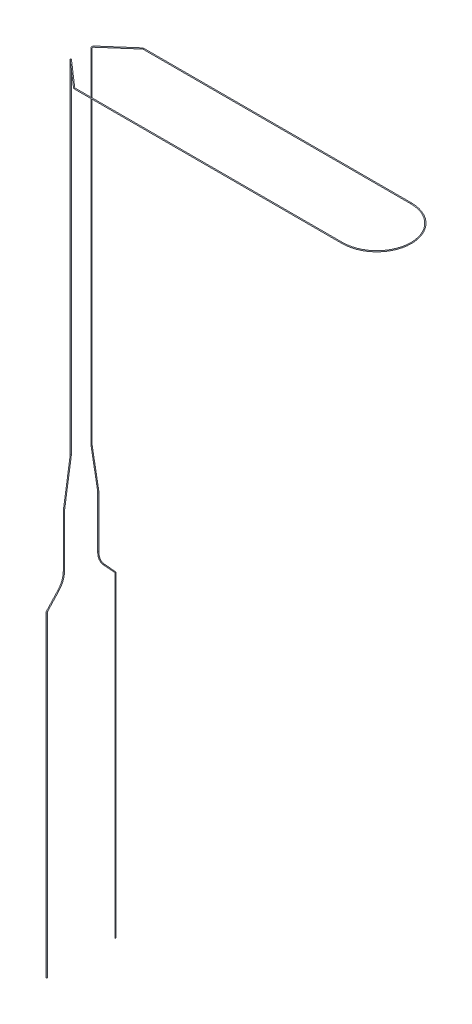
SolidWorks part; units mm, degrees
ref_plane "Plan de face" through (0, 0, 0) normal (0, 0, 1) x (1, 0, 0)
ref_plane "Plan de dessus" through (0, 0, 0) normal (0, 1, 0) x (1, 0, 0)
ref_plane "Plan de droite" through (0, 0, 0) normal (1, 0, 0) x (0, 0, -1)
sketch3d "Esquisse3D1"
  line L0 (0, 0, 0) -> (0, 0, 10.3571) construction
  line L6 (0, 255, 6) -> (0, 56.7647, 6)
  line L7 (0, 256, 6) -> (0, 256, 20) construction
  line L10 (0, 256, 20) -> (16, 256, 20) construction
  line L11 (0.7526, 256, 6.6585) -> (15.7172, 256, 19.7526)
  line L12 (0, 0, 0) -> (0, 256, 0) construction
  line L13 (16.3757, 256, 20) -> (172, 256, 20)
  line L14 (0, 256, 0) -> (219.9657, 256, 0) construction
  line L15 (0, 0, 5.3828) -> (0, -8.4495, 13.1824) construction
  line L16 (0, 0, 13.1824) -> (0, -8.4495, 13.1824) construction
  line L17 (0, -8.4495, 13.1824) -> (0, -15.5477, 19.7348)
  line L18 (0, 0, 10) -> (0, -0.31, 10)
  line L19 (0, -16.226, 20) -> (0, -200, 20)
  line L20 (0, 0, 10) -> (0, 29.2353, 10)
  line L21 (0, 30.7558, 9.8837) -> (0, 55.2442, 6.1163)
  line L22 (0, 0, -13.1824) -> (0, -8.4495, -13.1824) construction
  line L23 (0, 0, -5.3828) -> (0, -8.4495, -13.1824) construction
  line L24 (0, 256, -20) -> (16, 256, -20) construction
  line L25 (0, 256, -6) -> (0, 256, -20) construction
  line L26 (0, 30.7558, -9.8837) -> (0, 55.2442, -6.1163)
  line L27 (0, 0, -10) -> (0, 29.2353, -10)
  line L28 (0, -16.226, -20) -> (0, -200, -20)
  line L29 (0, 0, -10) -> (0, -0.31, -10)
  line L30 (0, -8.4495, -13.1824) -> (0, -15.5477, -19.7348)
  line L31 (16.3757, 256, -20) -> (172, 256, -20)
  line L32 (0.7526, 256, -6.6585) -> (15.7172, 256, -19.7526)
  line L33 (0, 255, -6) -> (0, 56.7647, -6)
  arc A0 (172, 256, 20) -> (172, 256, -20) centre (172, 256, 0) ccw
  circle A2 centre (20, 256, 20) radius 4 construction
  arc A3 (0, -0.31, 10) -> (0, -8.4495, 13.1824) centre (0, -0.31, 22) ccw
  arc A4 (16.3757, 256, 20) -> (15.7172, 256, 19.7526) centre (16.3757, 256, 19) ccw
  arc A5 (0, 29.2353, 10) -> (0, 30.7558, 9.8837) centre (0, 29.2353, 0) ccw
  arc A6 (0, -15.5477, 19.7348) -> (0, -16.226, 20) centre (0, -16.226, 19) ccw
  arc A7 (0, 56.7647, 6) -> (0, 55.2442, 6.1163) centre (0, 56.7647, 16) ccw
  arc A8 (0.7526, 256, 6.6585) -> (0, 255, 6) centre (0.7526, 255, 6.6585) ccw
  circle A9 centre (20, 256, -20) radius 4 construction
  arc A10 (0, 255, -6) -> (0.7526, 256, -6.6585) centre (0.7526, 255, -6.6585) cw
  arc A11 (0, 55.2442, -6.1163) -> (0, 56.7647, -6) centre (0, 56.7647, -16) cw
  arc A12 (0, -16.226, -20) -> (0, -15.5477, -19.7348) centre (0, -16.226, -19) cw
  arc A13 (0, 30.7558, -9.8837) -> (0, 29.2353, -10) centre (0, 29.2353, 0) cw
  arc A14 (15.7172, 256, -19.7526) -> (16.3757, 256, -20) centre (16.3757, 256, -19) cw
  arc A15 (0, -8.4495, -13.1824) -> (0, -0.31, -10) centre (0, -0.31, -22) cw
  point P13 (172, 276, 0)
  point P22 (20, 260, 20)
  point P25 (-12, -0.31, 22)
  point P28 (0, 30, 10)
  point P29 (16, 256, 20)
  point P31 (16.3757, 255, 19)
  point P34 (-10, 29.2353, 0)
  point P39 (0, -15.835, 20)
  point P40 (1, -16.226, 19)
  point P42 (0, 56, 6)
  point P44 (-10, 56.7647, 16)
  point P47 (0, 256, 6)
  point P48 (0.0941, 255, 7.4111)
  point P51 (20, 260, -20)
  point P61 (0.0941, 255, -7.4111)
  point P65 (-10, 56.7647, -16)
  point P69 (1, -16.226, -19)
  point P73 (-10, 29.2353, 0)
  point P77 (16.3757, 255, -19)
  point P80 (-12, -0.31, -22)
  point P83 (0, 56, -6)
  point P84 (0, -15.835, -20)
  point P85 (0, 30, -10)
  dimension "D3" = 20
  dimension "D4" = 8
  dimension "D8" = 12
  dimension "D12" = 1
  dimension "D15" = 10
  dimension "D16" = 10
  dimension "D17" = 1
  dimension "D2" = 20
  dimension "D5" = 172
  dimension "D13" = 30
  dimension "D6" = 6
  dimension "D7" = 47.29
  dimension "D9" = 20
  dimension "D10" = 0.31
  dimension "D11" = 200
  dimension "D14" = 200
  dimension "D18" = 256
  dimension "D19" = 10
sweep "Balayage1" add path "Esquisse3D1" circular profile diameter 0.5 parameters "D3"=0.5
